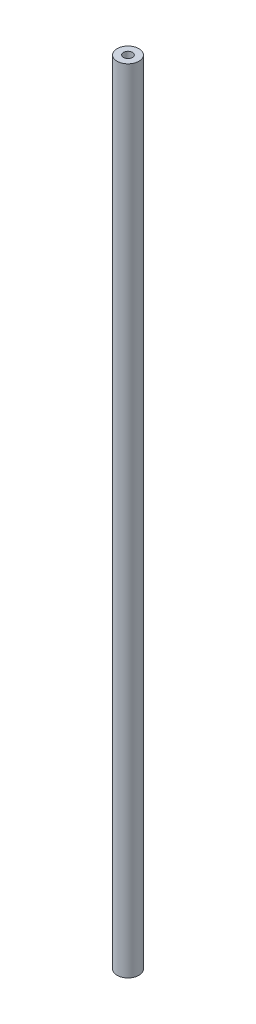
SolidWorks part; units mm, degrees
material "AISI 304"
ref_plane "Front Plane" through (0, 0, 0) normal (0, 0, 1) x (1, 0, 0)
ref_plane "Top Plane" through (0, 0, 0) normal (0, 1, 0) x (1, 0, 0)
ref_plane "Right Plane" through (0, 0, 0) normal (1, 0, 0) x (0, 0, -1)
sketch "Sketch3" plane through (0, 0, 0) normal (0, 1, 0) x (1, 0, 0)
  circle A0 centre (0, 0) radius 4
  dimension "D1" = 8
extrude "Boss-Extrude1" add sketch "Sketch3" along normal blind 290
hole_wizard "M4 Tapped Hole1" positions "Sketch5" profile "Sketch4" tap size "M4" standard "ISO"
sketch "Sketch5" plane through (0, 290, 0) normal (0, 1, 0) x (1, 0, 0)
  point P0 (0, 0)
sketch "Sketch4" plane through (0, 290, 0) normal (1, 0, 0) x (0, 0, 1)
  line L0 (0, 0) -> (0, 3.3914)
  line L1 (0, 3.3914) -> (1.65, 2.4)
  line L2 (1.65, 2.4) -> (1.65, 0)
  line L5 (1.65, 0) -> (0, 0)
  line L10 (0, 3.3914) -> (-1.65, 2.4) construction
  line L11 (0, -6.35) -> (0, 107.95) construction
  dimension "Tap Drill Dia." = 3.3
  dimension "Tap Drill Depth" = 2.4
  dimension "Drill Angle" = 118
cosmetic thread "Hole Thread1"
hole_wizard "M4 Tapped Hole2" positions "Sketch7" profile "Sketch6" tap size "M4" standard "ISO"
sketch "Sketch7" plane through (0, 0, 0) normal (0, -1, 0) x (-1, 0, 0)
  point P0 (0, 0)
sketch "Sketch6" plane through (0, 0, 0) normal (1, 0, 0) x (0, 0, -1)
  line L0 (0, 0) -> (0, 3.3914)
  line L1 (0, 3.3914) -> (1.65, 2.4)
  line L2 (1.65, 2.4) -> (1.65, 0)
  line L5 (1.65, 0) -> (0, 0)
  line L10 (0, 3.3914) -> (-1.65, 2.4) construction
  line L11 (0, -6.35) -> (0, 107.95) construction
  dimension "Tap Drill Dia." = 3.3
  dimension "Tap Drill Depth" = 2.4
  dimension "Drill Angle" = 118
cosmetic thread "Hole Thread2"
